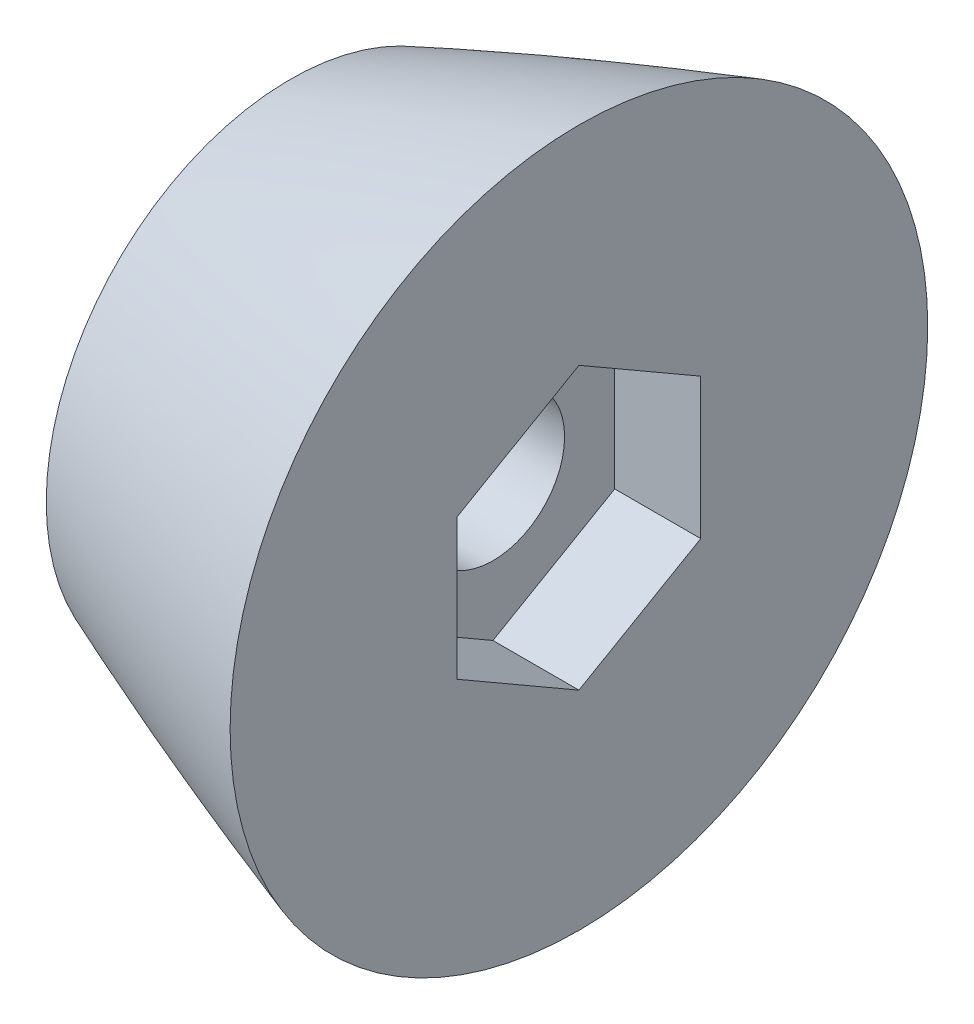
SolidWorks part; units mm, degrees
material "ABS"
ref_plane "Ebene vorne" through (0, 0, 0) normal (0, 0, 1) x (1, 0, 0)
ref_plane "Ebene oben" through (0, 0, 0) normal (0, 1, 0) x (1, 0, 0)
ref_plane "Ebene rechts" through (0, 0, 0) normal (1, 0, 0) x (0, 0, -1)
sketch "Skizze2" plane through (0, 0, 0) normal (0, 0, 1) x (1, 0, 0)
  line L0 (0, 0) -> (350.1385, 0)
  line L1 (350.1385, 0) -> (350.1385, 60.2) construction
  line L2 (350.1385, 0) -> (320.1385, 0)
  line L3 (320.1385, 0) -> (320.1385, 60.2)
  line L4 (320.1385, 60.2) -> (350.1385, 60.2)
  spline S0 degree 4 poles (0, 0) (0.0018, 0.0115) (0.0065, 0.0343) (0.0208, 0.0787) (0.0566, 0.1648) (0.1062, 0.2607) (0.1688, 0.3663) (0.2573, 0.5017) (0.3943, 0.6936) (0.6423, 1.0023) (1.0941, 1.4947) (1.8811, 2.2416) (3.223, 3.3515) (5.4849, 4.9778) (9.1312, 7.2558) (14.9211, 10.4012) (22.8871, 14.154) (35.1071, 19.2015) (51.1907, 24.8872) (70.2714, 30.6648) (92.146, 36.2979) (114.2022, 41.1638) (136.3963, 45.3527) (158.6965, 48.9292) (181.0797, 51.9412) (203.527, 54.428) (226.0231, 56.4233) (248.555, 57.9592) (271.1117, 59.0682) (293.6839, 59.7872) (316.2643, 60.1613) (333.2015, 60.2298) (344.4928, 60.2135) (350.1385, 60.2) knots 0 0 0 0 0 0.000129 0.000259 0.000518 0.001036 0.00133 0.001623 0.002316 0.003657 0.005731 0.00905 0.014375 0.023011 0.036694 0.056839 0.087619 0.120902 0.183695 0.246487 0.30928 0.372073 0.434866 0.497658 0.560451 0.623244 0.686036 0.748829 0.811622 0.874415 0.937207 1 1 1 1 1 construction
  spline S1 degree 4 poles (0, 0) (0.0018, 0.0115) (0.0065, 0.0343) (0.0208, 0.0787) (0.0566, 0.1648) (0.1062, 0.2607) (0.1688, 0.3663) (0.2573, 0.5017) (0.3943, 0.6936) (0.6423, 1.0023) (1.0941, 1.4947) (1.8811, 2.2416) (3.223, 3.3515) (5.4849, 4.9778) (9.1312, 7.2558) (14.9211, 10.4012) (22.8871, 14.154) (35.1071, 19.2015) (51.1907, 24.8872) (70.2714, 30.6648) (92.146, 36.2979) (114.2022, 41.1638) (136.3963, 45.3527) (158.6965, 48.9292) (181.0797, 51.9412) (203.527, 54.428) (226.0231, 56.4233) (248.555, 57.9592) (271.1117, 59.0682) (293.6839, 59.7872) (316.2643, 60.1613) (333.2015, 60.2298) (344.4928, 60.2135) (350.1385, 60.2) knots 0 0 0 0 0 0.000129 0.000259 0.000518 0.001036 0.00133 0.001623 0.002316 0.003657 0.005731 0.00905 0.014375 0.023011 0.036694 0.056839 0.087619 0.120902 0.183695 0.246487 0.30928 0.372073 0.434866 0.497658 0.560451 0.623244 0.686036 0.748829 0.811622 0.874415 0.937207 1 1 1 1 1
  dimension "D1" = 60.2
  dimension "D2" = 30
revolve "Rotation1" add sketch "Skizze2" angle 360 about L0
shell "Schale1" [suppressed] thickness 1
sketch "Skizze4" plane through (0, 0, 0) normal (1, 0, 0) x (0, 0, -1)
  circle A0 centre (0, 0) radius 60
  dimension "D1" = 120
extrude "Schnitt-Linear austragen2" cut sketch "Skizze4" along normal blind 30
sketch "Skizze7" plane through (320.1385, 0, 0) normal (1, 0, 0) x (0, 0, -1)
  circle A0 centre (0, 0) radius 100
  dimension "D1" = 200
extrude "Schnitt-Linear austragen4" cut sketch "Skizze7" against normal blind 270
sketch "Skizze5" [suppressed] plane through (0, 0, 0) normal (0, 0, 1) x (1, 0, 0)
  line L0 (15, -16.4088) -> (15, -5)
  line L1 (15, 10.4121) -> (15, -10.4121) construction
  line L2 (15, -5) -> (33, -5)
  line L3 (33, -5) -> (52.7309, -39.1749)
  line L4 (15, 11.5595) -> (15, -11.5595) construction
  line L5 (0, 0) -> (15, 0) construction
  spline S0 degree 2 poles (52.7309, -39.1749) (32.202, -30.4746) (15, -16.4088) knots 0 0 0 1 1 1
  dimension "D1" = 120
  dimension "D2" = 5
  dimension "D3" = 18
ref_plane "Ebene1" through (50.1385, 0, 0) normal (1, 0, 0) x (0, 0, -1)
sketch "Skizze6" plane through (50.1385, 0, 0) normal (1, 0, 0) x (0, 0, -1)
  line L1 (0, -9.815) -> (8.5, -4.9075)
  line L2 (8.5, -4.9075) -> (8.5, 4.9075)
  line L3 (8.5, 4.9075) -> (0, 9.815)
  line L4 (0, 9.815) -> (-8.5, 4.9075)
  line L5 (-8.5, 4.9075) -> (-8.5, -4.9075)
  line L6 (-8.5, -4.9075) -> (0, -9.815)
  circle A0 centre (0, 0) radius 8.5 construction
  dimension "D1" = 17
extrude "Schnitt-Linear austragen3" cut sketch "Skizze6" against normal blind 6 and the other way blind 20
sketch "Skizze8" plane through (44.1385, 0, 0) normal (1, 0, 0) x (0, 0, -1)
  circle A0 centre (0, 0) radius 5
  dimension "D1" = 10
extrude "Schnitt-Linear austragen5" cut sketch "Skizze8" against normal through all
equation "\"L\"= 350'length"
equation "\"C\"= 2 / 3'C-value"
